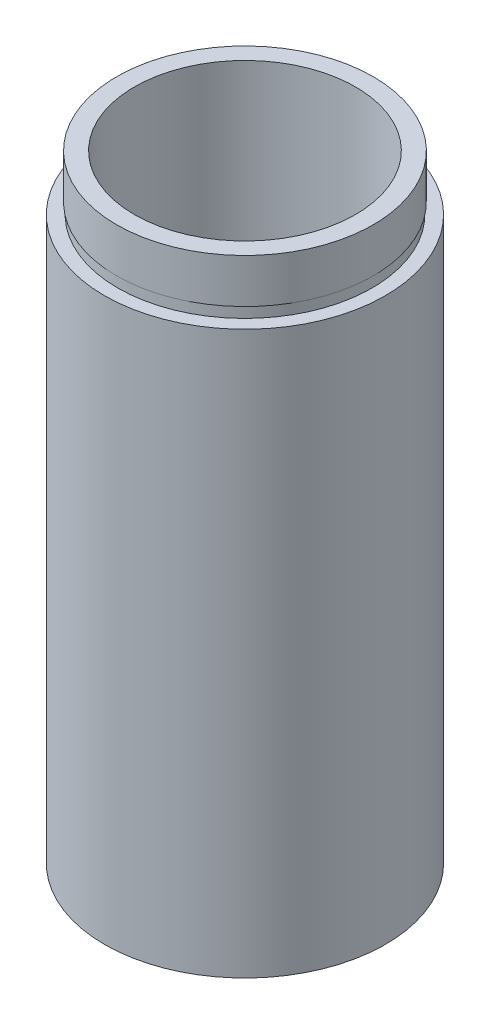
SolidWorks part; units mm, degrees
ref_plane "前视基准面" through (0, 0, 0) normal (0, 0, 1) x (1, 0, 0)
ref_plane "上视基准面" through (0, 0, 0) normal (0, 1, 0) x (1, 0, 0)
ref_plane "右视基准面" through (0, 0, 0) normal (1, 0, 0) x (0, 0, -1)
sketch "草图1" plane through (0, 0, 0) normal (0, 0, 1) x (1, 0, 0)
  line L0 (0, 161.3762) -> (0, 0) construction
  line L1 (141.7365, 0) -> (-131.7984, 0) construction
  line L2 (12.7, 0) -> (12.7, 50.8)
  line L3 (11.1, 4.5) -> (11.7, 4.5)
  line L4 (11.1, 0) -> (12.7, 0)
  line L5 (11.7, 4.5) -> (11.7, 5.5)
  line L6 (10, 5.5) -> (10, 55.8)
  line L7 (11.1, 4.5) -> (11.1, 0)
  line L8 (11.7, 5.5) -> (10, 5.5)
  line L9 (11.5, 51.8) -> (11.5, 50.8)
  line L10 (12.7, 50.8) -> (11.5, 50.8)
  line L11 (11.6, 51.8) -> (11.6, 55.8)
  line L12 (11.5, 51.8) -> (11.6, 51.8)
  line L13 (11.6, 55.8) -> (10, 55.8)
  dimension "D2" = 12.7
  dimension "D3" = 11.7
  dimension "D4" = 10
  dimension "D5" = 11.5
  dimension "D6" = 11.6
  dimension "D7" = 1
  dimension "D8" = 50.8
  dimension "D9" = 5
  dimension "D10" = 1
  dimension "D11" = 11.1
  dimension "D12" = 4.5
revolve "旋转1" add sketch "草图1" angle 360 about L0
cosmetic thread "装饰螺纹线1" parameters "D2"=23.2
cosmetic thread "装饰螺纹线2" parameters "D2"=21
cosmetic thread "装饰螺纹线3" parameters "D2"=23
